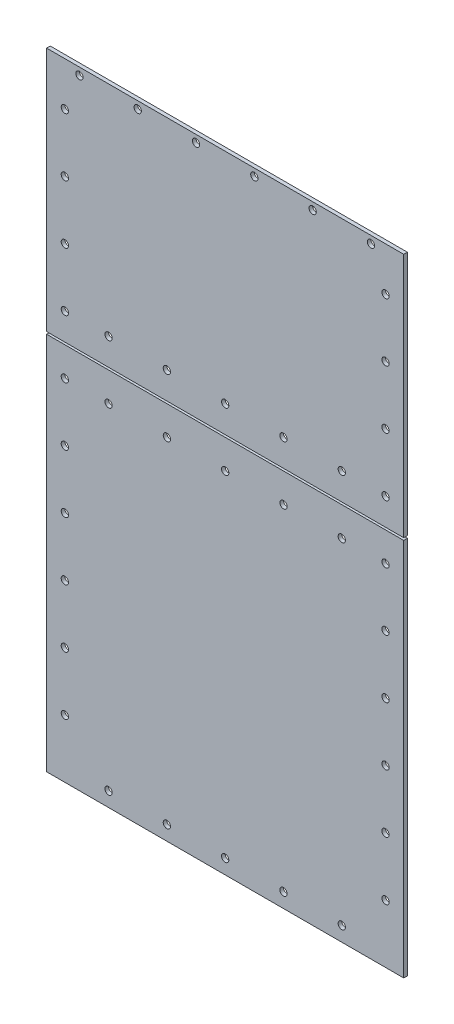
SolidWorks part; units mm, degrees
other "Markup1"
sketch "Sketch2" plane through (0, -273.05, 1.5875) normal (0, 0, 1) x (1, 0, 0)
material "Copper"
ref_plane "Front Plane" through (0, 0, 0) normal (0, 0, 1) x (1, 0, 0)
ref_plane "Top Plane" through (0, 0, 0) normal (0, 1, 0) x (1, 0, 0)
ref_plane "Right Plane" through (0, 0, 0) normal (1, 0, 0) x (0, 0, -1)
sketch "Sketch1" plane through (0, 0, 0) normal (0, 0, 1) x (1, 0, 0)
  line L0 (0, -106.95) -> (155.58, -106.95)
  line L1 (0, 0) -> (155.58, 0)
  line L2 (0, 0) -> (0, -273.05)
  line L3 (0, -273.05) -> (155.58, -273.05)
  line L4 (155.58, 0) -> (155.58, -273.05)
  line L5 (0, -107.95) -> (155.58, -107.95)
  circle A0 centre (7.94, -19.05) radius 1.5875
  circle A1 centre (147.64, -19.05) radius 1.5875
  circle A2 centre (147.64, -44.45) radius 1.5875
  circle A3 centre (147.64, -69.85) radius 1.5875
  circle A4 centre (147.64, -95.25) radius 1.5875
  circle A5 centre (147.64, -120.65) radius 1.5875
  circle A6 centre (147.64, -146.05) radius 1.5875
  circle A7 centre (147.64, -171.45) radius 1.5875
  circle A8 centre (147.64, -196.85) radius 1.5875
  circle A9 centre (147.64, -222.25) radius 1.5875
  circle A10 centre (147.64, -247.65) radius 1.5875
  circle A11 centre (7.94, -44.45) radius 1.5875
  circle A12 centre (7.94, -69.85) radius 1.5875
  circle A13 centre (7.94, -95.25) radius 1.5875
  circle A14 centre (7.94, -120.65) radius 1.5875
  circle A15 centre (7.94, -146.05) radius 1.5875
  circle A16 centre (7.94, -171.45) radius 1.5875
  circle A17 centre (7.94, -196.85) radius 1.5875
  circle A18 centre (7.94, -222.25) radius 1.5875
  circle A19 centre (7.94, -247.65) radius 1.5875
  circle A20 centre (14.29, -3.175) radius 1.5875
  circle A21 centre (39.69, -3.175) radius 1.5875
  circle A22 centre (65.09, -3.175) radius 1.5875
  circle A23 centre (90.49, -3.175) radius 1.5875
  circle A24 centre (115.89, -3.175) radius 1.5875
  circle A25 centre (141.29, -3.175) radius 1.5875
  circle A26 centre (26.987, -266.7) radius 1.5875
  circle A27 centre (52.387, -266.7) radius 1.5875
  circle A28 centre (77.787, -266.7) radius 1.5875
  circle A29 centre (103.187, -266.7) radius 1.5875
  circle A30 centre (128.587, -266.7) radius 1.5875
  circle A31 centre (26.99, -95.25) radius 1.5875
  circle A32 centre (52.39, -95.25) radius 1.5875
  circle A33 centre (77.79, -95.25) radius 1.5875
  circle A34 centre (103.19, -95.25) radius 1.5875
  circle A35 centre (128.59, -95.25) radius 1.5875
  circle A36 centre (26.99, -120.65) radius 1.5875
  circle A37 centre (52.39, -120.65) radius 1.5875
  circle A38 centre (77.79, -120.65) radius 1.5875
  circle A39 centre (103.19, -120.65) radius 1.5875
  circle A40 centre (128.59, -120.65) radius 1.5875
  point P85 (0, 0)
  dimension "D3" = 3.175
  dimension "D1" = 155.58
  dimension "D2" = 273.05
  dimension "D4" = 19.05
  dimension "D5" = 7.94
  dimension "D8" = 25.4
  dimension "D9" = 7.94
  dimension "D10" = 3.175
  dimension "D11" = 14.29
  dimension "D13" = 25.4
  dimension "D14" = 6.35
  dimension "D15" = 26.987
  dimension "D17" = 25.4
  dimension "D18" = 11.7
  dimension "D19" = 1
  dimension "D21" = 26.99
  dimension "D23" = 25.4
  dimension "D24" = 26.99
  dimension "D25" = 25.4
  dimension "D27" = 25.4
  dimension "D6" = 2
  dimension "D7" = 10
  dimension "D12" = 6
  dimension "D16" = 5
  dimension "D22" = 5
  dimension "D26" = 5
extrude "Boss-Extrude1" add sketch "Sketch1" along normal blind 1.5875 contours L4 L1 L2 L0 A25 A24 A23 A22 A21 A20 A13 A12 A11 A4 A3 A2 A1 A0 | L4 L0 L2 L3 A30 A29 A28 A27 A26 A19 A18 A17 A16 A15 A14 A10 A9 A8 A7 A6 A5
equation "\"D9@Sketch1\"=\"D5@Sketch1\""
equation "\"D18@Sketch1\"=\"D8@Sketch1\"/2-1"
